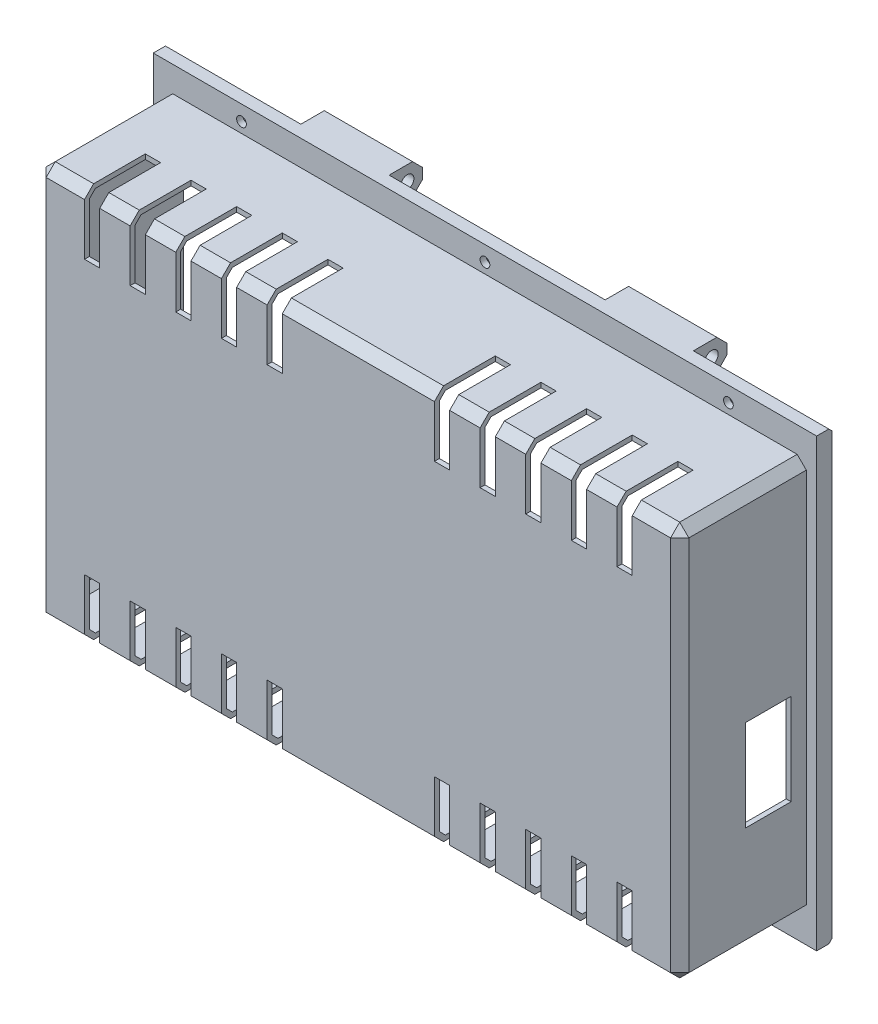
SolidWorks part; units mm, degrees
ref_plane "Alzado" through (0, 0, 0) normal (0, 0, 1) x (1, 0, 0)
ref_plane "Planta" through (0, 0, 0) normal (0, 1, 0) x (1, 0, 0)
ref_plane "Vista lateral" through (0, 0, 0) normal (1, 0, 0) x (0, 0, -1)
sketch "Croquis1" plane through (0, 0, 0) normal (0, 0, 1) x (1, 0, 0)
  line L1 (-105.6, 64.87) -> (105.6, 64.87)
  line L2 (-105.6, 64.87) -> (-105.6, -64.87)
  line L3 (-105.6, -64.87) -> (105.6, -64.87)
  line L4 (105.6, 64.87) -> (105.6, -64.87)
  line L5 (-105.6, 64.87) -> (105.6, -64.87) construction
  line L6 (-105.6, -64.87) -> (105.6, 64.87) construction
  line L7 (-104, 63.27) -> (104, 63.27)
  line L8 (-104, 63.27) -> (-104, -63.27)
  line L9 (-104, -63.27) -> (104, -63.27)
  line L10 (104, 63.27) -> (104, -63.27)
  line L11 (-104, 63.27) -> (104, -63.27) construction
  line L12 (-104, -63.27) -> (104, 63.27) construction
  point P0 (0, 0)
  point P6 (0, 0)
  dimension "D1" = 211.2
  dimension "D2" = 129.74
  dimension "D3" = 1.6
  dimension "D4" = 1.6
extrude "Saliente-Extruir1" add sketch "Croquis1" along normal blind 40
sketch "Croquis2" plane through (0, 0, 0) normal (0, 0, -1) x (-1, 0, 0)
  line L1 (-109, 73.27) -> (109, 73.27)
  line L2 (-109, 73.27) -> (-109, -73.27)
  line L3 (-109, -73.27) -> (109, -73.27)
  line L4 (109, 73.27) -> (109, -73.27)
  line L5 (-109, 73.27) -> (109, -73.27) construction
  line L6 (-109, -73.27) -> (109, 73.27) construction
  line L7 (-104, 63.27) -> (104, 63.27)
  line L8 (-104, 63.27) -> (-104, -63.27)
  line L9 (-104, -63.27) -> (104, -63.27)
  line L10 (104, 63.27) -> (104, -63.27)
  line L11 (-104, 63.27) -> (104, -63.27) construction
  line L12 (-104, -63.27) -> (104, 63.27) construction
  point P1 (0, 0)
  point P6 (0, 0)
  dimension "D1" = 10
  dimension "D2" = 5
extrude "Saliente-Extruir2" add sketch "Croquis2" along normal blind 5
sketch "Croquis7" plane through (0, 0, -5) normal (0, 0, -1) x (-1, 0, 0)
  line L0 (0, 0) -> (0, 50000) construction
  line L1 (0, 0) -> (50000, 0) construction
  line L2 (0, 68.27) -> (50000, 68.27) construction
  line L3 (104, 64.2122) -> (104, -49935.7878) construction
  line L4 (109, 73.27) -> (-109, 73.27) construction
  line L5 (109, -73.27) -> (109, 73.27) construction
  circle A0 centre (0, 68.27) radius 1.6
  circle A4 centre (80, 68.27) radius 1.6
  circle A5 centre (-80, 68.27) radius 1.6
  circle A9 centre (-80, -68.27) radius 1.6
  circle A10 centre (80, -68.27) radius 1.6
  circle A12 centre (0, -68.27) radius 1.6
  dimension "D3" = 3.2
  dimension "D1" = 5
  dimension "D2" = 5
  dimension "D4" = 160
extrude "Cortar-Extruir3" cut sketch "Croquis7" against normal through all
sketch "Croquis8" plane through (0, 0, -5) normal (0, 0, -1) x (-1, 0, 0)
  circle A0 centre (-80, 68.27) radius 2.75
  circle A1 centre (0, 68.27) radius 2.75
  circle A2 centre (80, 68.27) radius 2.75
  circle A3 centre (80, -68.27) radius 2.75
  circle A4 centre (0, -68.27) radius 2.75
  circle A5 centre (-80, -68.27) radius 2.75
  dimension "D1" = 5.5
extrude "Cortar-Extruir4" cut sketch "Croquis8" against normal blind 3
sketch "Croquis9" plane through (0, 0, 0) normal (1, 0, 0) x (0, 0, -1)
  line L0 (5, 48.8595) -> (5, 50048.8595) construction
  line L2 (0, 0) -> (50000, 0) construction
  line L3 (5, 73.27) -> (50005, 73.27) construction
  line L4 (39.8778, 68.27) -> (-49960.1222, 68.27) construction
  line L5 (5, 73.27) -> (14.7518, 73.27)
  line L6 (14.7518, 73.27) -> (15, 73.27)
  line L7 (15, 73.27) -> (15, 63.27)
  line L8 (15, 63.27) -> (5, 63.27)
  line L9 (5, 63.27) -> (5, 73.27)
  circle A0 centre (10, 68.27) radius 2.15
  dimension "D2" = 4.3
  dimension "D1" = 5
  dimension "D3" = 5
  dimension "D4" = 10
  dimension "D5" = 10
extrude "Saliente-Extruir3" add sketch "Croquis9" along normal blind 29 from offset 35.5
chamfer "Chaflán3" distance 3.3 angle 45 2 edges at (50, 63.27, -15) (50, 73.27, -15)
mirror "Simetría2" about plane through (0, 0, 0) normal (1, 0, 0) of "Saliente-Extruir3", "Chaflán3"
chamfer "Chaflán2" distance 1 angle 45 4 edges at (0, -73.27, -5) (86.75, 73.27, -5) (-86.75, 73.27, -5) (0, 73.27, -5)
sketch "Croquis10" plane through (0, 0, 40) normal (0, 0, 1) x (1, 0, 0)
  line L1 (-105.6, 64.87) -> (105.6, 64.87)
  line L2 (-105.6, 64.87) -> (-105.6, -64.87)
  line L3 (-105.6, -64.87) -> (105.6, -64.87)
  line L4 (105.6, 64.87) -> (105.6, -64.87)
  line L5 (-105.6, 64.87) -> (105.6, -64.87) construction
  line L6 (-105.6, -64.87) -> (105.6, 64.87) construction
  point P4 (0, 0)
extrude "Saliente-Extruir4" add sketch "Croquis10" along normal blind 1.6
chamfer "Chaflán4" distance 2 angle 45 8 edges at (-104, 0, 40) (-104, -63.27, 17.5) (0, -63.27, 40) (104, -63.27, 17.5) (104, 0, 40) (-104, 63.27, 17.5) (0, 63.27, 40) (104, 63.27, 17.5)
chamfer "Chaflán5" distance 3 angle 45 8 edges at (0, 64.87, 41.6) (105.6, 64.87, 20.8) (105.6, 0, 41.6) (105.6, -64.87, 20.8) (0, -64.87, 41.6) (-105.6, 64.87, 20.8) (-105.6, 0, 41.6) (-105.6, -64.87, 20.8)
sketch "Croquis11" plane through (0, 0, 0) normal (1, 0, 0) x (0, 0, -1)
  line L0 (-38.6, 64.87) -> (0, 64.87) construction
  line L1 (-21.6, 64.87) -> (-41.6, 64.87)
  line L2 (-21.6, 64.87) -> (-21.6, 44.87)
  line L3 (-21.6, 44.87) -> (-41.6, 44.87)
  line L4 (-41.6, 64.87) -> (-41.6, 44.87)
  line L5 (-21.6, 64.87) -> (-41.6, 44.87) construction
  line L6 (-21.6, 44.87) -> (-41.6, 64.87) construction
  line L7 (-41.6, -61.87) -> (-41.6, 61.87) construction
  point P4 (-31.6, 54.87)
  dimension "D1" = 20
  dimension "D2" = 20
extrude "Cortar-Extruir5" cut sketch "Croquis11" against normal blind 5 from offset 30
pattern_linear "MatrizL1" count 5 spacing 15 along (1, 0, 0) of "Cortar-Extruir5"
mirror "Simetría3" about plane through (0, 0, 0) normal (1, 0, 0) of "MatrizL1", "Cortar-Extruir5"
mirror "Simetría4" about plane through (0, 0, 0) normal (0, 1, 0) of "Simetría3", "Cortar-Extruir5", "MatrizL1"
sketch "Croquis12" plane through (-105.6, 0, 0) normal (-1, 0, 0) x (0, 0, 1)
  line L0 (0, 61.87) -> (0, -61.87) construction
  line L1 (5, 0) -> (20, 0)
  line L2 (5, 0) -> (5, -30)
  line L3 (5, -30) -> (20, -30)
  line L4 (20, 0) -> (20, -30)
  line L5 (5, 0) -> (20, -30) construction
  line L6 (5, -30) -> (20, 0) construction
  point P4 (12.5, -15)
  dimension "D1" = 5
  dimension "D2" = 15
  dimension "D3" = 30
extrude "Cortar-Extruir6" cut sketch "Croquis12" against normal through all
